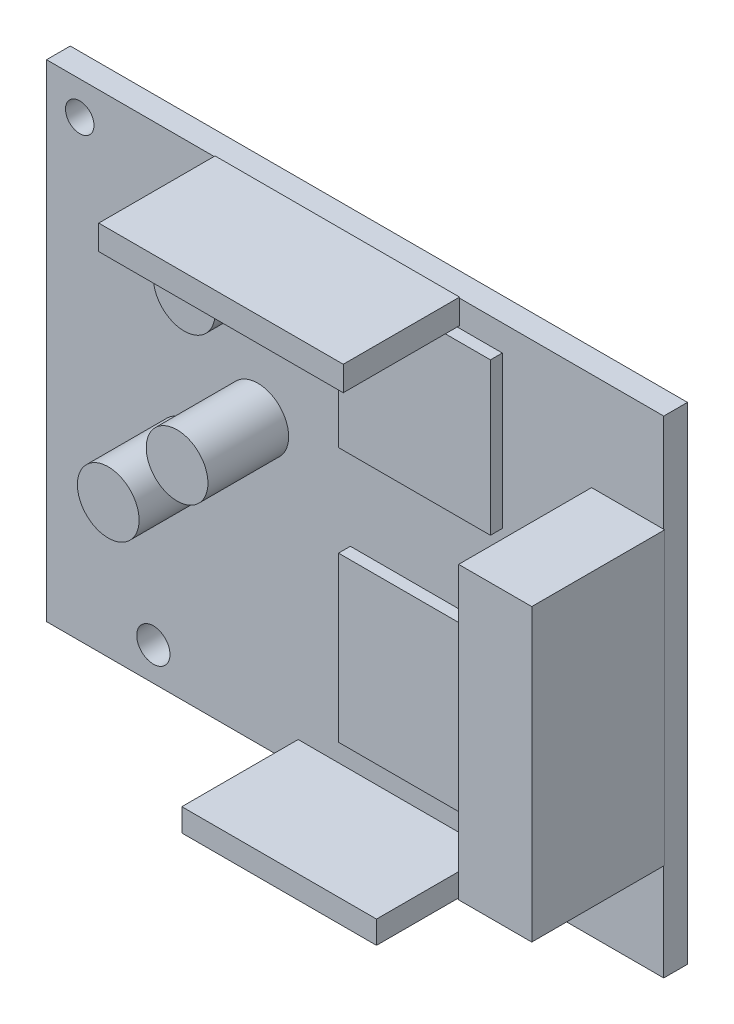
SolidWorks part; units mm, degrees
ref_plane "Front Plane" through (0, 0, 0) normal (0, 0, 1) x (1, 0, 0)
ref_plane "Top Plane" through (0, 0, 0) normal (0, 1, 0) x (1, 0, 0)
ref_plane "Right Plane" through (0, 0, 0) normal (1, 0, 0) x (0, 0, -1)
sketch "Sketch1" plane through (0, 0, 0) normal (0, 0, 1) x (1, 0, 0)
  circle A0 centre (-17.5, -3) radius 3.25
extrude "Boss-Extrude1" add sketch "Sketch1" along normal blind 8.5
sketch "Sketch3" plane through (0, 0, 0) normal (0, 0, 1) x (1, 0, 0)
  line L1 (32.5, -25.625) -> (-32.5, -25.625)
  line L2 (32.5, -25.625) -> (32.5, 25.625)
  line L3 (32.5, 25.625) -> (-32.5, 25.625)
  line L4 (-32.5, -25.625) -> (-32.5, 25.625)
  line L5 (32.5, -25.625) -> (-32.5, 25.625) construction
  line L6 (32.5, 25.625) -> (-32.5, -25.625) construction
  point P0 (0, 0)
extrude "Boss-Extrude2" add sketch "Sketch3" against normal blind 2.5
sketch "Sketch4" plane through (0, 0, 0) normal (0, 0, 1) x (1, 0, 0)
  line L1 (32.5, -15.3) -> (24.9, -15.3)
  line L2 (32.5, -15.3) -> (32.5, 15.3)
  line L3 (32.5, 15.3) -> (24.9, 15.3)
  line L4 (24.9, -15.3) -> (24.9, 15.3)
  line L5 (32.5, -15.3) -> (24.9, 15.3) construction
  line L6 (32.5, 15.3) -> (24.9, -15.3) construction
  point P0 (30.5, 0)
extrude "Boss-Extrude3" add sketch "Sketch4" along normal blind 14
sketch "Sketch5" plane through (0, 0, 0) normal (0, 0, 1) x (1, 0, 0)
  circle A0 centre (-10.25, 4) radius 3.25
extrude "Boss-Extrude4" add sketch "Sketch5" along normal blind 8.5
sketch "Sketch6" plane through (0, 0, 0) normal (0, 0, 1) x (1, 0, 0)
  line L0 (32.5, 25.625) -> (-32.5, 25.625) construction
  line L1 (-14.75, 25.625) -> (11, 25.625)
  line L2 (-14.75, 25.625) -> (-14.75, 23.125)
  line L3 (-14.75, 23.125) -> (11, 23.125)
  line L4 (11, 25.625) -> (11, 23.125)
extrude "Boss-Extrude5" add sketch "Sketch6" along normal blind 12.25
sketch "Sketch8" plane through (0, 0, 0) normal (0, 0, 1) x (1, 0, 0)
  circle A0 centre (-9.5, 19.87) radius 3.25
extrude "Boss-Extrude9" add sketch "Sketch8" along normal blind 8.5 contours A0
sketch "Sketch9" plane through (0, 0, 0) normal (0, 0, 1) x (1, 0, 0)
  line L0 (-32.5, -25.625) -> (32.5, -25.625) construction
  line L1 (-6, -23.125) -> (14.5, -23.125)
  line L2 (-6, -23.125) -> (-6, -25.625)
  line L3 (-6, -25.625) -> (14.5, -25.625)
  line L4 (14.5, -23.125) -> (14.5, -25.625)
extrude "Boss-Extrude10" add sketch "Sketch9" along normal blind 12.25
sketch "Sketch10" plane through (0, -25.625, 0) normal (0, -1, 0) x (1, 0, 0)
  line L1 (-6, 12.25) -> (14.5, 12.25)
  line L2 (-6, 12.25) -> (-6, 0)
  line L3 (-6, 0) -> (14.5, 0)
  line L4 (14.5, 12.25) -> (14.5, 0)
extrude "Cut-Extrude1" cut sketch "Sketch10" against normal blind 0.1
sketch "Sketch12" plane through (0, 25.625, 0) normal (0, 1, 0) x (1, 0, 0)
  line L1 (11, -12.25) -> (-14.75, -12.25)
  line L2 (11, -12.25) -> (11, 0)
  line L3 (11, 0) -> (-14.75, 0)
  line L4 (-14.75, -12.25) -> (-14.75, 0)
extrude "Boss-Extrude11" add sketch "Sketch12" along normal blind 0.1
sketch "Sketch14" plane through (32.5, 0, 0) normal (1, 0, 0) x (0, 0, -1)
  line L1 (-14, 15.3) -> (0, 15.3)
  line L2 (-14, 15.3) -> (-14, -15.3)
  line L3 (-14, -15.3) -> (0, -15.3)
  line L4 (0, 15.3) -> (0, -15.3)
extrude "Boss-Extrude12" add sketch "Sketch14" along normal blind 0.1
sketch "Sketch15" plane through (0, 0, 0) normal (0, 0, 1) x (1, 0, 0)
  circle A0 centre (-29, 22.125) radius 1.5
extrude "Cut-Extrude2" cut sketch "Sketch15" against normal through all
sketch "Sketch16" plane through (0, 0, 0) normal (0, 0, 1) x (1, 0, 0)
  circle A0 centre (-21.25, -22.125) radius 1.75
extrude "Cut-Extrude3" cut sketch "Sketch16" against normal through all
sketch "Sketch17" plane through (0, 0, 0) normal (0, 0, 1) x (1, 0, 0)
  line L1 (-0.5, 22.875) -> (15.5, 22.875)
  line L2 (-0.5, 22.875) -> (-0.5, 6.875)
  line L3 (-0.5, 6.875) -> (15.5, 6.875)
  line L4 (15.5, 22.875) -> (15.5, 6.875)
extrude "Boss-Extrude13" add sketch "Sketch17" along normal blind 1.25
sketch "Sketch18" plane through (0, 0, 0) normal (0, 0, 1) x (1, 0, 0)
  line L1 (-0.5, -2.75) -> (15.5, -2.75)
  line L2 (-0.5, -2.75) -> (-0.5, -20)
  line L3 (-0.5, -20) -> (15.5, -20)
  line L4 (15.5, -2.75) -> (15.5, -20)
extrude "Boss-Extrude14" add sketch "Sketch18" along normal blind 1.25
